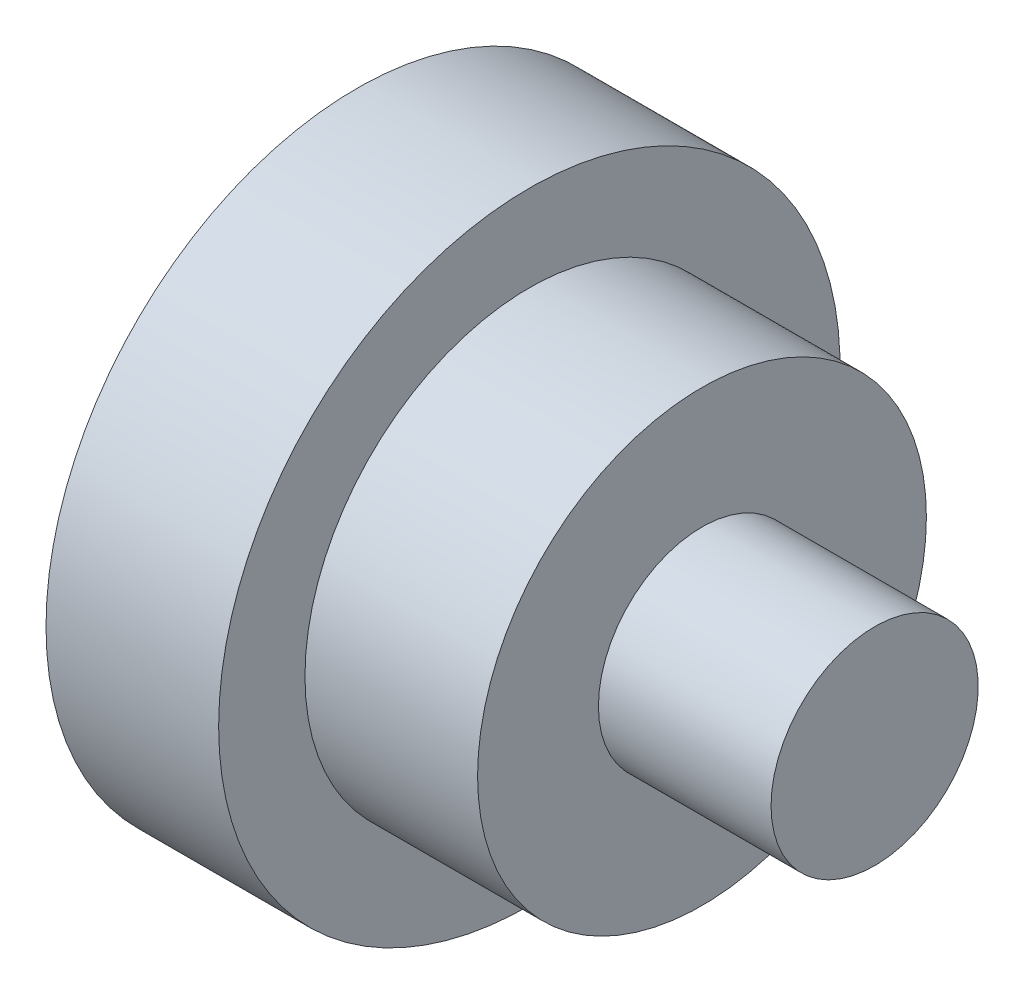
SolidWorks part; units mm, degrees
ref_plane "前视基准面" through (0, 0, 0) normal (0, 0, 1) x (1, 0, 0)
ref_plane "上视基准面" through (0, 0, 0) normal (0, 1, 0) x (1, 0, 0)
ref_plane "右视基准面" through (0, 0, 0) normal (1, 0, 0) x (0, 0, -1)
sketch "草图2" plane through (0, 0, 0) normal (0, 0, 1) x (1, 0, 0)
  line L0 (0, 0) -> (6.9634, 0) construction
  line L1 (0, 0) -> (0, 6.5)
  line L2 (0, 6.5) -> (5, 6.5)
  line L3 (5, 6.5) -> (5, 3)
  line L4 (5, 3) -> (10, 3)
  line L5 (10, 3) -> (10, 0)
  line L6 (10, 0) -> (0, 0)
  dimension "D1" = 6
  dimension "D2" = 13
  dimension "D3" = 5
  dimension "D4" = 5
revolve "旋转1" add sketch "草图2" angle 360 about L0
sketch "草图3" plane through (0, 0, 0) normal (-1, 0, 0) x (0, 0, 1)
  circle A0 centre (0, 0) radius 9
  dimension "D1" = 18
extrude "凸台-拉伸1" add sketch "草图3" along normal blind 5
sketch "草图4" plane through (-5, 0, 0) normal (-1, 0, 0) x (0, 0, 1)
  circle A0 centre (0, 0) radius 5
  dimension "D1" = 10
extrude "切除-拉伸1" cut sketch "草图4" against normal blind 8
